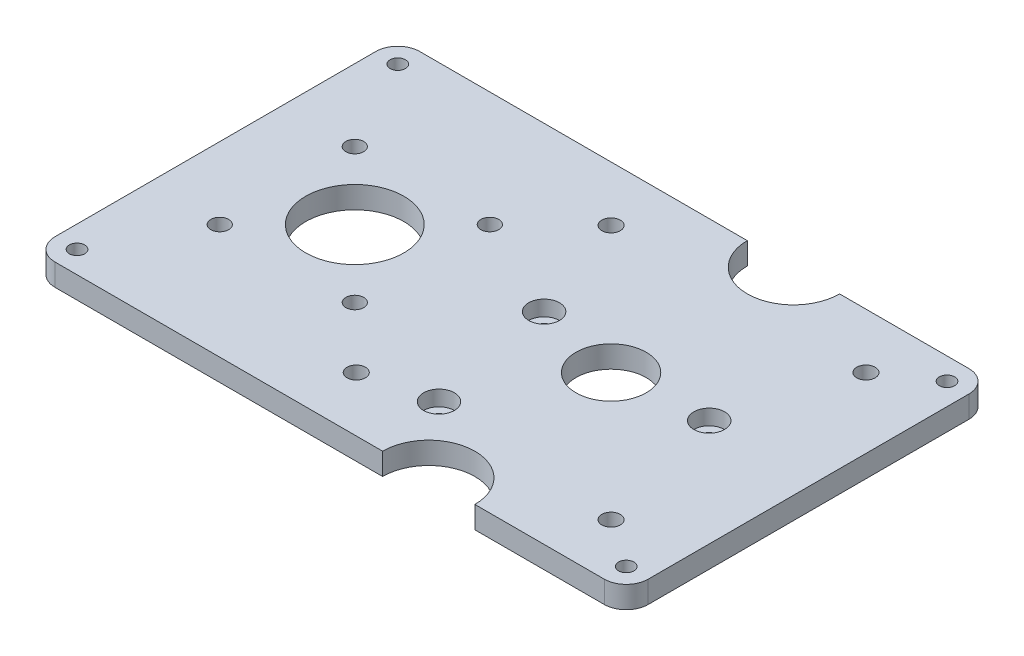
SolidWorks part; units mm, degrees
ref_plane "Front Plane" through (0, 0, 0) normal (0, 0, 1) x (1, 0, 0)
ref_plane "Top Plane" through (0, 0, 0) normal (0, 1, 0) x (1, 0, 0)
ref_plane "Right Plane" through (0, 0, 0) normal (1, 0, 0) x (0, 0, -1)
sketch "Sketch1" plane through (0, 0, 0) normal (0, 1, 0) x (1, 0, 0)
  line L0 (-67.5, 0) -> (67.5, 0) construction
  line L1 (67.5, -41.5) -> (33.05, -41.5)
  line L2 (67.5, -41.5) -> (67.5, 41.5)
  line L3 (67.5, 41.5) -> (33.05, 41.5)
  line L4 (-67.5, -41.5) -> (-67.5, 41.5)
  line L5 (67.5, -41.5) -> (-67.5, 41.5) construction
  line L6 (67.5, 41.5) -> (-67.5, -41.5) construction
  line L7 (22.55, 31.1) -> (22.55, -31.1) construction
  line L8 (49.455, -31.1) -> (-49.455, -31.1) construction
  line L9 (49.455, -31.1) -> (49.455, 31.1) construction
  line L10 (49.455, 31.1) -> (-49.455, 31.1) construction
  line L11 (-49.455, -31.1) -> (-49.455, 31.1) construction
  line L12 (49.455, -31.1) -> (-49.455, 31.1) construction
  line L13 (49.455, 31.1) -> (-49.455, -31.1) construction
  line L14 (0, 41.5) -> (0, -41.5) construction
  line L15 (12.05, -41.5) -> (-67.5, -41.5)
  line L16 (-51.147, -15.367) -> (-20.413, -15.367) construction
  line L17 (-51.147, -15.367) -> (-51.147, 15.367) construction
  line L18 (-51.147, 15.367) -> (-20.413, 15.367) construction
  line L19 (-20.413, -15.367) -> (-20.413, 15.367) construction
  line L20 (-51.147, -15.367) -> (-20.413, 15.367) construction
  line L21 (-51.147, 15.367) -> (-20.413, -15.367) construction
  line L22 (12.05, 41.5) -> (-67.5, 41.5)
  circle A0 centre (-6.45, 29) radius 2.1
  circle A1 centre (51.55, 29) radius 2.1
  circle A2 centre (51.55, -29) radius 2.1
  circle A3 centre (-6.45, -29) radius 2.1
  circle A4 centre (22.55, 0) radius 8
  circle A6 centre (-35.78, 0) radius 11.176
  circle A8 centre (-62.5, 36.5) radius 1.75
  circle A9 centre (62.5, 36.5) radius 1.75
  circle A10 centre (62.5, -36.5) radius 1.75
  circle A11 centre (-62.5, -36.5) radius 1.75
  circle A12 centre (-20.413, 15.367) radius 2.032
  circle A13 centre (-20.413, -15.367) radius 2.032
  circle A14 centre (-51.147, -15.367) radius 2.032
  circle A15 centre (-51.147, 15.367) radius 2.032
  arc A16 (33.05, -41.5) -> (12.05, -41.5) centre (22.55, -41.5) ccw
  arc A17 (12.05, 41.5) -> (33.05, 41.5) centre (22.55, 41.5) ccw
  point P0 (0, 0)
  point P13 (22.55, 0)
  point P18 (0, 0)
  point P27 (22.55, 0)
  dimension "D3" = 4.2
  dimension "D4" = 16
  dimension "D8" = 22.352
  dimension "D9" = 30.734
  dimension "D17" = 3.5
  dimension "D19" = 5
  dimension "D12" = 4.064
  dimension "D20" = 4.064
  dimension "D21" = 4.064
  dimension "D22" = 4.064
  dimension "D23" = 21
  dimension "D24" = 21
  dimension "D1" = 135
  dimension "D2" = 83
  dimension "D5" = 29
  dimension "D6" = 29
  dimension "D7" = 29
  dimension "D10" = 58.33
  dimension "D11" = 30.734
  dimension "D13" = 98.91
  dimension "D14" = 62.2
  dimension "D15" = 72.005
  dimension "D16" = 98.91
  dimension "D18" = 5
extrude "Boss-Extrude1" add sketch "Sketch1" along normal blind 5
sketch "Sketch3" plane through (0, 5, 0) normal (0, 1, 0) x (1, 0, 0)
  line L1 (-29.93, -5.85) -> (-52.93, -5.85)
  line L2 (-29.93, -5.85) -> (-29.93, 5.85)
  line L3 (-29.93, 5.85) -> (-52.93, 5.85)
  line L4 (-52.93, -5.85) -> (-52.93, 5.85)
  line L5 (-29.93, 0) -> (-41.63, 0) construction
  circle A2 centre (-35.78, 0) radius 5.85 construction
  circle A3 centre (-35.78, 0) radius 11.176 construction
  circle A4 centre (-27.43, 0) radius 1
  circle A5 centre (-56.43, 0) radius 1
  dimension "D3" = 11.7
  dimension "D2" = 2
  dimension "D5" = 2
  dimension "D1" = 23
  dimension "D4" = 2.5
  dimension "D6" = 3.5
extrude "Cut-Extrude1" [suppressed] cut sketch "Sketch3" against normal through all
sketch "Sketch4" [suppressed] plane through (0, 5, 0) normal (0, 1, 0) x (1, 0, 0)
  line L0 (-45.3026, 5.85) -> (-52.93, 5.85) construction
  line L1 (-52.93, -5.85) -> (-45.3026, -5.85) construction
  line L2 (-29.93, -5.85) -> (-29.93, 5.85) construction
  circle A0 centre (-35.78, 0) radius 5.85
sketch "Sketch5" plane through (0, 5, 0) normal (0, 1, 0) x (1, 0, 0)
  line L1 (-10.0733, -32.5804) -> (55.1733, -32.5804)
  line L2 (-10.0733, -32.5804) -> (-10.0733, 32.5804)
  line L3 (-10.0733, 32.5804) -> (55.1733, 32.5804)
  line L4 (55.1733, -32.5804) -> (55.1733, 32.5804)
  line L5 (-10.0733, -32.5804) -> (55.1733, 32.5804) construction
  line L6 (-10.0733, 32.5804) -> (55.1733, -32.5804) construction
  circle A0 centre (22.55, 0) radius 31.4571
  point P0 (22.55, 0)
  circle M1 centre (-51.147, 15.367) radius 2.032
  circle M2 centre (-51.147, -15.367) radius 2.032
  circle M3 centre (-20.413, -15.367) radius 2.032
  circle M4 centre (-20.413, 15.367) radius 2.032
  circle M5 centre (62.5, 36.5) radius 1.75
  circle M6 centre (-62.5, 36.5) radius 1.75
  line M7 (67.5, -41.5) -> (67.5, 41.5)
  line M9 (67.5, 41.5) -> (33.05, 41.5)
  line M11 (-67.5, 41.5) -> (-67.5, -41.5)
  line M13 (33.05, -41.5) -> (67.5, -41.5)
  circle M19 centre (22.55, 0) radius 8
  circle M20 centre (-35.78, 0) radius 11.176
  circle M21 centre (62.5, -36.5) radius 1.75
  circle M22 centre (-62.5, -36.5) radius 1.75
  arc M30 (33.05, 41.5) -> (12.05, 41.5) centre (22.55, 41.5) cw
  line M31 (12.05, 41.5) -> (-67.5, 41.5)
  line M32 (-67.5, -41.5) -> (12.05, -41.5)
  arc M33 (12.05, -41.5) -> (33.05, -41.5) centre (22.55, -41.5) cw
extrude "Cut-Extrude2" [suppressed] cut sketch "Sketch5" against normal blind 10 contours L2 L3 L1 M30 M31 M11 M32 M33 M2 M4 M6 M20 M22 M3 M1 | A0 M33 M30 M19 | L4 L1 L3 M33 M13 M7 M9 M30 M5 M21
fillet "Fillet1" radius 5 4 edges at (-67.5, 2.5, 41.5) (-67.5, 2.5, -41.5) (67.5, 2.5, 41.5) (67.5, 2.5, -41.5)
sketch "Sketch8" plane through (0, 5, 0) normal (0, 1, 0) x (1, 0, 0)
  circle A7 centre (43.1993, 1.6821) radius 1.65
  circle A8 centre (2.9215, 4.384) radius 1.65
  circle A9 centre (8.6993, -25.3179) radius 1.65
  dimension "D1" = 3.3
  dimension "D2" = 3.3
  dimension "D3" = 3.3
extrude "Cut-Extrude3" cut sketch "Sketch8" against normal blind 10 contours A7 | A8 | A9
sketch "Sketch9" plane through (0, 5, 0) normal (0, 1, 0) x (1, 0, 0)
  circle A0 centre (43.1993, 1.6821) radius 3.5
  circle A1 centre (8.6993, -25.3179) radius 3.5
  circle A2 centre (2.9215, 4.384) radius 3.5
  circle M1 centre (43.1993, 1.6821) radius 1.65
  circle M2 centre (2.9215, 4.384) radius 1.65
  circle M3 centre (8.6993, -25.3179) radius 1.65
  dimension "D1" = 7
  dimension "D2" = 7
  dimension "D3" = 7
extrude "Cut-Extrude4" cut sketch "Sketch9" against normal blind 3.5 contours A2 M2 | A1 M3 | A0 M1
sketch "Sketch10" [suppressed] plane through (0, 5, 0) normal (0, 1, 0) x (1, 0, 0)
  line L1 (28.0899, 32.5804) -> (15.0541, 32.5804)
  line L2 (28.0899, 32.5804) -> (28.0899, 31.1354)
  line L3 (28.0899, 31.1354) -> (15.0541, 31.1354)
  line L4 (15.0541, 32.5804) -> (15.0541, 31.1354)
  line L5 (28.0899, -32.5804) -> (15.0541, -32.5804)
  line L6 (28.0899, -32.5804) -> (28.0899, -31.3439)
  line L7 (28.0899, -31.3439) -> (15.0541, -31.3439)
  line L8 (15.0541, -32.5804) -> (15.0541, -31.3439)
extrude "Boss-Extrude2" [suppressed] add sketch "Sketch10" against normal through all
